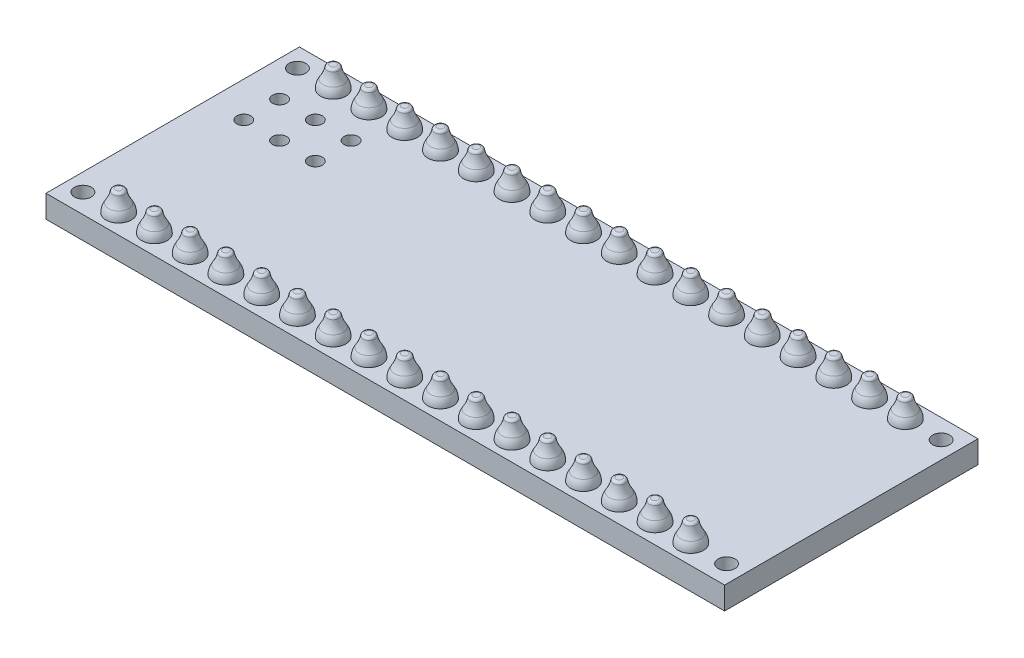
SolidWorks part; units mm, degrees
material "E-Glass Fiber"
ref_plane "Front Plane" through (0, 0, 0) normal (0, 0, 1) x (1, 0, 0)
ref_plane "Top Plane" through (0, 0, 0) normal (0, 1, 0) x (1, 0, 0)
ref_plane "Right Plane" through (0, 0, 0) normal (1, 0, 0) x (0, 0, -1)
sketch "Sketch1" plane through (0, 0, 0) normal (0, 1, 0) x (1, 0, 0)
  line L0 (0, 7.62) -> (-3.78, 7.62) construction
  line L1 (-3.78, 16.62) -> (44.42, 16.62)
  line L2 (-3.78, 16.62) -> (-3.78, -1.38)
  line L3 (-3.78, -1.38) -> (44.42, -1.38)
  line L4 (44.42, 16.62) -> (44.42, -1.38)
  line L5 (0, 0) -> (40.64, 0) construction
  line L6 (0, 0) -> (0, 15.24) construction
  line L7 (0, 15.24) -> (40.64, 15.24) construction
  line L8 (40.64, 0) -> (40.64, 15.24) construction
  line L10 (40.64, 7.62) -> (44.42, 7.62) construction
  circle A0 centre (-2.54, 0) radius 0.6
  circle A1 centre (-2.54, 15.24) radius 0.6
  circle A2 centre (43.18, 15.24) radius 0.6
  circle A3 centre (43.18, 0) radius 0.6
  dimension "D5" = 1.2
  dimension "D1" = 48.2
  dimension "D2" = 18
  dimension "D3" = 15.24
  dimension "D4" = 40.64
  dimension "D6" = 2.54
  dimension "D7" = 2.54
  dimension "D8" = 3.78
  dimension "D9" = 3.78
extrude "Boss-Extrude2" add sketch "Sketch1" along normal blind 1.6
sketch "Sketch2" plane through (0, 0, 0) normal (0, 1, 0) x (1, 0, 0)
  line L0 (0, -0.88) -> (0, 0.88) construction
  line L2 (-0.88, 0) -> (0.88, 0) construction
  circle A0 centre (0, 0) radius 0.45
  circle A1 centre (0, 15.24) radius 0.45
  dimension "D1" = 0.9
  dimension "D2" = 15.24
extrude "Cut-Extrude2" cut sketch "Sketch2" along normal blind 1.6
pattern_linear "LPattern1" count 17 spacing 2.54 along (1, 0, 0) of "Cut-Extrude2"
sketch "Sketch3" plane through (0, 0, 0) normal (0, 1, 0) x (1, 0, 0)
  line L1 (-0.88, 0) -> (0.88, 0) construction
  circle A0 centre (1.27, 12.7) radius 0.5
  circle A1 centre (-1.27, 12.7) radius 0.5
  circle A2 centre (-1.27, 10.16) radius 0.5
  circle A3 centre (3.81, 12.7) radius 0.5
  circle A4 centre (3.81, 10.16) radius 0.5
  circle A5 centre (1.27, 10.16) radius 0.5
  circle A6 centre (0, 15.24) radius 0.45 construction
  dimension "D1" = 1
  dimension "D5" = 10.16
  dimension "D7" = 2.54
  dimension "D2" = 2.54
  dimension "D3" = 2.54
  dimension "D4" = 1.27
  dimension "D6" = 2.54
extrude "Cut-Extrude4" cut sketch "Sketch3" along normal blind 1.6
sketch "Sketch6" plane through (0, 0, 0) normal (1, 0, 0) x (0, 0, -1)
  line L0 (0, 1.6) -> (0.9, 1.6)
  line L1 (-1.38, 1.6) -> (16.62, 1.6) construction
  line L2 (0.2252, 3.1) -> (0, 3.1)
  line L3 (0, 0.88) -> (0, -0.88) construction
  line L4 (0, 3.1) -> (0, 1.6)
  line L5 (0, 1.3722) -> (0, 3.4408) construction
  arc A0 (0.9, 1.6) -> (0.7139, 2.2122) centre (-0.2, 1.6) ccw
  arc A1 (0.7139, 2.2122) -> (0.4221, 2.9352) centre (2.2924, 3.2697) cw
  arc A2 (0.4221, 2.9352) -> (0.2252, 3.1) centre (0.2252, 2.9) ccw
  point P16 (0.4, 3.1)
  dimension "D4" = 1.1
  dimension "D5" = 1.9
  dimension "D6" = 0.2
  dimension "D1" = 1.5
  dimension "D2" = 0.8
  dimension "D3" = 1.8
revolve "Revolve1" add sketch "Sketch6" angle 360 about L5
pattern_linear "LPattern2" count 2 spacing 15.24 along (0, 0, -1) count 17 spacing 2.54 along (1, 0, 0) of "Revolve1"
ref_plane "Plane3" through (0, 0, -10.16) normal (0, 0, 1) x (1, 0, 0)
sketch "Sketch7" plane through (0, 0, -10.16) normal (0, 0, 1) x (1, 0, 0)
  line L0 (-1.27, 3.889) -> (-1.27, -2.5597) construction
  line L2 (0, -1.705) -> (0, 1.705) construction
  line L3 (-1.27, 0) -> (-0.37, 0)
  line L4 (9.9, 0) -> (-9.9, 0) construction
  line L5 (-1.27, 0) -> (-1.27, -1.5)
  line L6 (-1.27, -1.5) -> (-1.0575, -1.5)
  arc A0 (-0.859, -1.325) -> (-0.59, -0.66) centre (0.53, -1.5) cw
  arc A1 (-0.59, -0.66) -> (-0.37, 0) centre (-1.47, 0) ccw
  arc A2 (-1.0575, -1.5) -> (-0.859, -1.325) centre (-1.0575, -1.3) ccw
  point P16 (-0.87, -1.5)
  dimension "D5" = 1.1
  dimension "D6" = 0.2
  dimension "D1" = 1.27
  dimension "D2" = 1.5
  dimension "D3" = 0.8
  dimension "D4" = 1.8
revolve "Revolve2" add sketch "Sketch7" angle 360 about L0
sketch "Sketch9" plane through (0, 0, 0) normal (0, 1, 0) x (1, 0, 0)
  line L0 (-1.705, 0) -> (1.705, 0) construction
  line L1 (44.42, -1.38) -> (44.42, 16.62) construction
  circle A0 centre (40.37, 5.42) radius 0.4
  circle A1 centre (40.37, 9.82) radius 0.4
  dimension "D1" = 0.8
  dimension "D2" = 4.4
  dimension "D3" = 5.42
  dimension "D4" = 4.05
extrude "Cut-Extrude6" [suppressed] cut sketch "Sketch9" along normal blind 10
pattern_linear "LPattern3" count 2 spacing 2.54 along (0, 0, -1) count 3 spacing 2.54 along (1, 0, 0) of "Revolve2"
